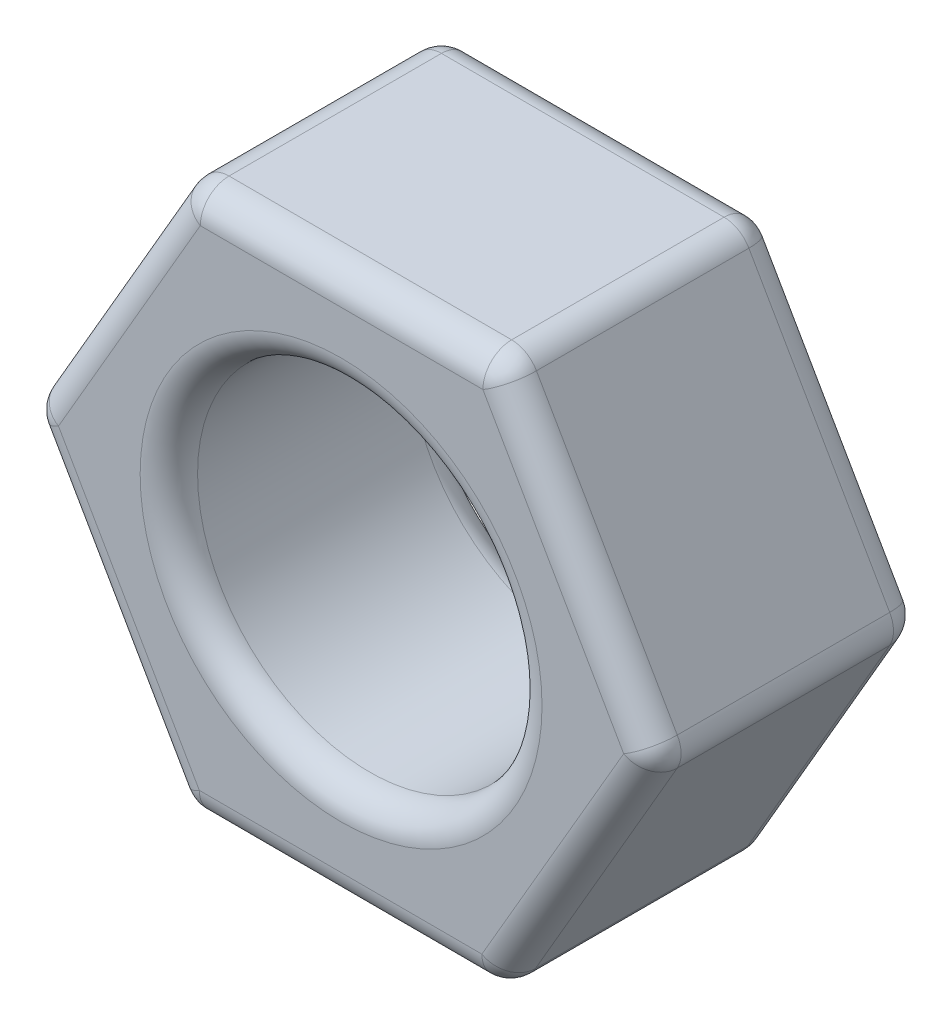
SolidWorks part; units mm, degrees
ref_plane "Спереди" through (0, 0, 0) normal (0, 0, 1) x (1, 0, 0)
ref_plane "Сверху" through (0, 0, 0) normal (0, 1, 0) x (1, 0, 0)
ref_plane "Справа" through (0, 0, 0) normal (1, 0, 0) x (0, 0, -1)
sketch "Sketch1" plane through (0, 0, 0) normal (0, 0, 1) x (1, 0, 0)
  line L1 (-2.7403, 4.7687) -> (-5.5, 0.0111)
  line L2 (-5.5, 0.0111) -> (-2.7596, -4.7576)
  line L3 (-2.7596, -4.7576) -> (2.7403, -4.7687)
  line L4 (2.7403, -4.7687) -> (5.5, -0.0111)
  line L5 (5.5, -0.0111) -> (2.7596, 4.7576)
  line L6 (2.7596, 4.7576) -> (-2.7403, 4.7687)
  circle A0 centre (0, 0) radius 5.5 construction
  circle A1 centre (0, 0) radius 3
  dimension "D1" = 11
  dimension "D2" = 6
extrude "Boss-Extrude1" add sketch "Sketch1" along normal blind 4.7
fillet "Fillet1" radius 0.5 20 edges at (-2.7403, 4.7687, 2.35) (5.5, -0.0111, 2.35) (2.7596, 4.7576, 2.35) (3, 0, 0) (-4.1202, 2.3899, 0) (4.1202, -2.3899, 0) (4.1298, 2.3732, 0) (0.0096, 4.7631, 0) (3, 0, 4.7) (4.1298, 2.3732, 4.7) (4.1202, -2.3899, 4.7) (-4.1202, 2.3899, 4.7) (0.0096, 4.7631, 4.7) (-0.0096, -4.7631, 4.7) (2.7403, -4.7687, 2.35) (-0.0096, -4.7631, 0) (-5.5, 0.0111, 2.35) (-4.1298, -2.3732, 4.7) (-2.7596, -4.7576, 2.35) (-4.1298, -2.3732, 0)
